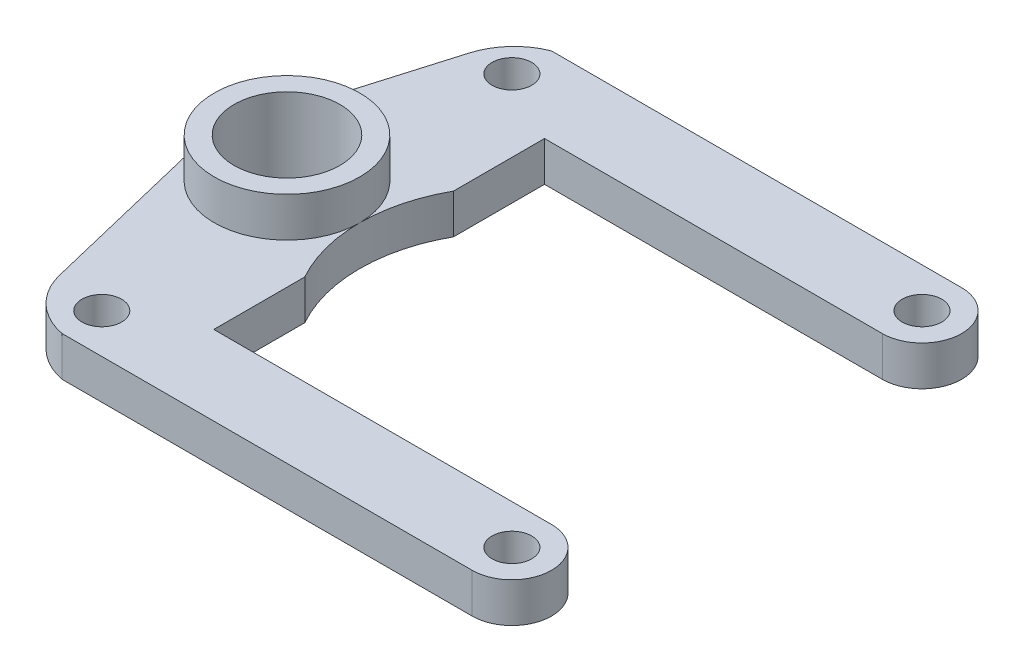
SolidWorks part; units mm, degrees
ref_plane "Front Plane" through (0, 0, 0) normal (0, 0, 1) x (1, 0, 0)
ref_plane "Top Plane" through (0, 0, 0) normal (0, 1, 0) x (1, 0, 0)
ref_plane "Right Plane" through (0, 0, 0) normal (1, 0, 0) x (0, 0, -1)
sketch "Sketch1" plane through (0, 0, 0) normal (0, 1, 0) x (1, 0, 0)
  line L0 (0, 0) -> (0, 31) construction
  line L1 (0, 31) -> (31, 31) construction
  line L2 (31, 31) -> (31, 0) construction
  line L3 (31, 0) -> (0, 0) construction
  line L4 (5.4671, 31) -> (5.4671, -3) construction
  line L5 (31, -3) -> (0, -3)
  line L6 (31, 28) -> (5.4671, 28)
  line L7 (31, 34) -> (0, 34)
  line L8 (0, 31) -> (31, 0) construction
  line L9 (15.5, 15.5) -> (-17.2117, 15.5) construction
  line L10 (-7.4849, 15.5) -> (-3.9171, 0.7358)
  line L11 (-7.4849, 15.5) -> (-2.9746, 30.7603)
  line L12 (31, 3) -> (5.4671, 3)
  line L13 (5.4671, 3) -> (5.4671, 28)
  circle A0 centre (0, 31) radius 1.5
  circle A1 centre (31, 31) radius 1.5
  circle A2 centre (31, 0) radius 1.5
  circle A3 centre (0, 0) radius 1.5
  arc A4 (31, 3) -> (31, -3) centre (31, 0) cw
  arc A5 (31, 28) -> (31, 34) centre (31, 31) ccw
  circle A6 centre (-1.5, 15.5) radius 4
  arc A7 (-3.9171, 0.7358) -> (0, -3) centre (0.943, 1.9103) ccw
  arc A8 (-2.9746, 30.7603) -> (0, 34) centre (1.8203, 29.3431) cw
  point P21 (-1.5, 15.5)
  dimension "D3" = 3
  dimension "D9" = 8
  dimension "D4" = 5
  dimension "D6" = 5
  dimension "D1" = 31
  dimension "D2" = 31
  dimension "D5" = 3
  dimension "D7" = 3
  dimension "D8" = 17
extrude "Boss-Extrude1" add sketch "Sketch1" along normal blind 3
sketch "Sketch2" plane through (0, 3, 0) normal (0, 1, 0) x (1, 0, 0)
  line L0 (0, 31) -> (31, 0) construction
  circle A0 centre (15.5, 15.5) radius 11.5
  dimension "D1" = 23
extrude "Cut-Extrude2" cut sketch "Sketch2" against normal blind 3
sketch "Sketch3" plane through (0, 3, 0) normal (0, 1, 0) x (1, 0, 0)
  circle A0 centre (-1.5, 15.5) radius 4
  circle A1 centre (-1.5, 15.5) radius 5.5
extrude "Boss-Extrude2" add sketch "Sketch3" along normal blind 3
